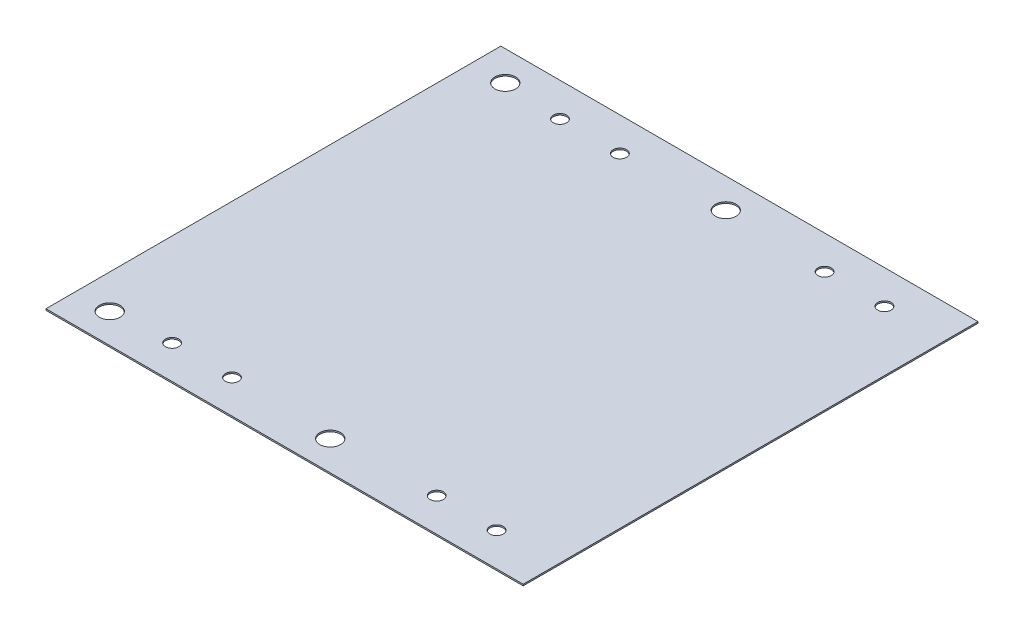
SolidWorks part; units mm, degrees
ref_plane "Front Plane" through (0, 0, 0) normal (0, 0, 1) x (1, 0, 0)
ref_plane "Top Plane" through (0, 0, 0) normal (0, 1, 0) x (1, 0, 0)
ref_plane "Right Plane" through (0, 0, 0) normal (1, 0, 0) x (0, 0, -1)
sketch "Sketch1" plane through (0, 0, 0) normal (0, 1, 0) x (1, 0, 0)
  line L1 (-40.25, 38.3675) -> (40.25, 38.3675)
  line L2 (-40.25, 38.3675) -> (-40.25, -38.3675)
  line L3 (-40.25, -38.3675) -> (40.25, -38.3675)
  line L4 (40.25, 38.3675) -> (40.25, -38.3675)
  line L5 (-40.25, 38.3675) -> (40.25, -38.3675) construction
  line L6 (-40.25, -38.3675) -> (40.25, 38.3675) construction
  circle A0 centre (-34.5, 33.3675) radius 1.75
  circle A1 centre (-24.62, 32.7175) radius 1.125
  circle A2 centre (-14.52, 32.7175) radius 1.125
  circle A3 centre (2.7, 33.3675) radius 1.75
  circle A4 centre (20.02, 32.7175) radius 1.125
  circle A5 centre (30.12, 32.7175) radius 1.125
  circle A6 centre (-34.5, -33.3675) radius 1.75
  circle A7 centre (2.7, -33.3675) radius 1.75
  circle A8 centre (-24.62, -32.7175) radius 1.125
  circle A9 centre (-14.52, -32.7175) radius 1.125
  circle A10 centre (20.02, -32.7175) radius 1.125
  circle A11 centre (30.12, -32.7175) radius 1.125
  point P0 (0, 0)
  dimension "D3" = 3.5
  dimension "D4" = 2.25
  dimension "D1" = 76.735
  dimension "D2" = 80.5
  dimension "D5" = 5.65
  dimension "D6" = 5.65
  dimension "D7" = 5
  dimension "D8" = 5
  dimension "D9" = 5.75
  dimension "D10" = 9.88
  dimension "D11" = 10.1
  dimension "D12" = 10.1
  dimension "D13" = 27.32
  dimension "D14" = 17.32
extrude "Boss-Extrude1" add sketch "Sketch1" along normal blind 0.25
